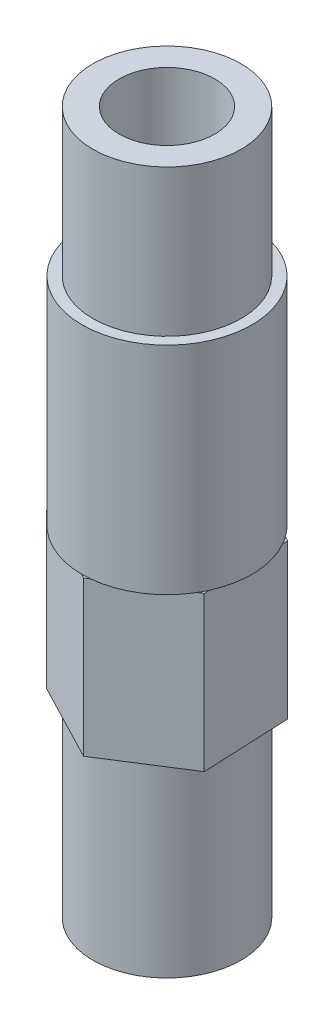
SolidWorks part; units mm, degrees
ref_plane "Спереди" through (0, 0, 0) normal (0, 0, 1) x (1, 0, 0)
ref_plane "Сверху" through (0, 0, 0) normal (0, 1, 0) x (1, 0, 0)
ref_plane "Справа" through (0, 0, 0) normal (1, 0, 0) x (0, 0, -1)
sketch "Эскиз2" plane through (0, 0, 0) normal (0, 1, 0) x (1, 0, 0)
  circle A0 centre (0, 0) radius 4.8
extrude "Бобышка-Вытянуть1" add sketch "Эскиз2" along normal blind 12
sketch "Эскиз3" plane through (0, 12, 0) normal (0, 1, 0) x (1, 0, 0)
  line L7 (5.0208, -2.6086) -> (4.7695, 3.0439)
  line L8 (4.7695, 3.0439) -> (-0.2513, 5.6524)
  line L9 (-0.2513, 5.6524) -> (-5.0208, 2.6086)
  line L10 (-5.0208, 2.6086) -> (-4.7695, -3.0439)
  line L11 (-4.7695, -3.0439) -> (0.2513, -5.6524)
  line L12 (0.2513, -5.6524) -> (5.0208, -2.6086)
  circle A0 centre (0, 0) radius 4.9 construction
extrude "Бобышка-Вытянуть2" add sketch "Эскиз3" along normal blind 10
sketch "Эскиз4" plane through (0, 22, 0) normal (0, 1, 0) x (1, 0, 0)
  circle A0 centre (0, 0) radius 5.5
extrude "Бобышка-Вытянуть3" add sketch "Эскиз4" along normal blind 14
sketch "Эскиз5" plane through (0, 36, 0) normal (0, 1, 0) x (1, 0, 0)
  circle A0 centre (0, 0) radius 4.8
extrude "Бобышка-Вытянуть4" add sketch "Эскиз5" along normal blind 9.5
sketch "Эскиз6" plane through (0, 45.5, 0) normal (0, 1, 0) x (1, 0, 0)
  circle A0 centre (0, 0) radius 3.1
extrude "Вырез-Вытянуть1" cut sketch "Эскиз6" against normal through all
